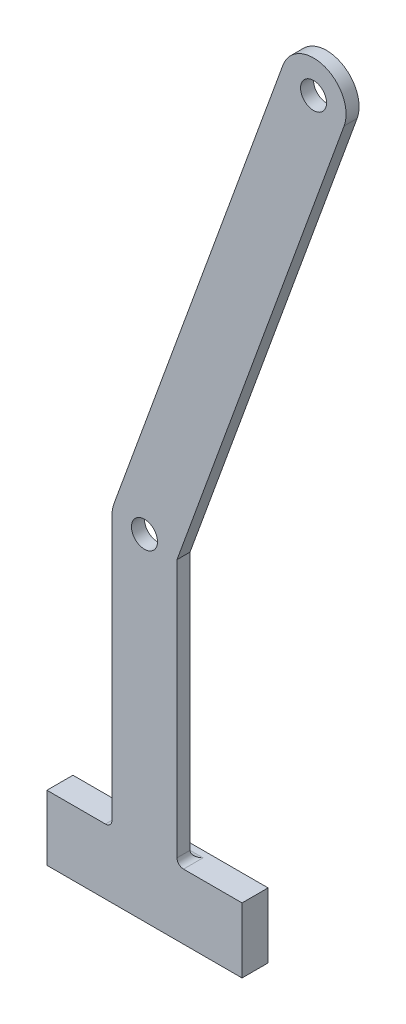
SolidWorks part; units mm, degrees
ref_plane "Front Plane" through (0, 0, 0) normal (0, 0, 1) x (1, 0, 0)
ref_plane "Top Plane" through (0, 0, 0) normal (0, 1, 0) x (1, 0, 0)
ref_plane "Right Plane" through (0, 0, 0) normal (1, 0, 0) x (0, 0, -1)
sketch "Sketch1" plane through (0, 0, 0) normal (0, 0, 1) x (1, 0, 0)
  line L0 (-76.2, 0) -> (-76.2, -95.25) construction
  line L1 (-27.94, -19.05) -> (-124.46, -19.05) construction
  line L2 (-27.94, -19.05) -> (-27.94, -171.45) construction
  line L3 (-27.94, -171.45) -> (-124.46, -171.45) construction
  line L4 (-124.46, -19.05) -> (-124.46, -171.45) construction
  line L5 (-27.94, -19.05) -> (-124.46, -171.45) construction
  line L6 (-27.94, -171.45) -> (-124.46, -19.05) construction
  line L7 (0, 0) -> (-76.2, 0) construction
  line L8 (-27.94, -19.05) -> (-60.9518, -109.7491) construction
  line L9 (-21.973, -21.2218) -> (-54.9847, -111.921)
  line L10 (-33.907, -16.8782) -> (-66.9188, -107.5773)
  line L11 (-27.94, -19.05) -> (-20.32, -19.05) construction
  line L12 (-60.9518, -19.05) -> (-60.9518, -162.56) construction
  line L13 (-67.3018, -109.7491) -> (-67.3018, -162.56)
  line L14 (-54.6018, -109.7491) -> (-54.6018, -162.56)
  line L15 (-67.3018, -162.56) -> (-80.0018, -162.56)
  line L16 (-80.0018, -162.56) -> (-80.0018, -175.26)
  line L17 (-80.0018, -175.26) -> (-41.9018, -175.26)
  line L18 (-41.9018, -175.26) -> (-41.9018, -162.56)
  line L19 (-41.9018, -162.56) -> (-54.6018, -162.56)
  circle A0 centre (-27.94, -19.05) radius 2.54
  circle A1 centre (-124.46, -19.05) radius 2.54
  circle A2 centre (-124.46, -171.45) radius 2.54
  circle A3 centre (-27.94, -171.45) radius 2.54
  circle A4 centre (-60.9518, -109.7491) radius 2.54
  circle A5 centre (-27.94, -19.05) radius 6.35
  circle A6 centre (-60.9518, -109.7491) radius 6.35
  dimension "D4" = 5.08
  dimension "D6" = 5.08
  dimension "D9" = 3.81
  dimension "D10" = 5.08
  dimension "D11" = 3.81
  dimension "D1" = 95.25
  dimension "D2" = 76.2
  dimension "D3" = 152.4
  dimension "D5" = 96.52
  dimension "D7" = 96.52
  dimension "D8" = 20
  dimension "D12" = 7.62
  dimension "D13" = 143.51
  dimension "D14" = 38.1
  dimension "D15" = 12.7
  dimension "D16" = 12.7
extrude "Boss-Extrude1" add sketch "Sketch1" along normal blind 2.54 contours A6 L9 A5 L10 | A5 A0 | A6 A4 | A6 L13 L15 L16 L17 L18 L19 L14 L9 | A6 L9 L14
sketch "Sketch2" plane through (0, 0, 0) normal (0, 0, -1) x (-1, 0, 0)
  line L1 (41.9018, -162.56) -> (80.0018, -162.56)
  line L2 (41.9018, -162.56) -> (41.9018, -175.26)
  line L3 (41.9018, -175.26) -> (80.0018, -175.26)
  line L4 (80.0018, -162.56) -> (80.0018, -175.26)
  line L5 (41.9018, -162.56) -> (80.0018, -175.26) construction
  line L6 (41.9018, -175.26) -> (80.0018, -162.56) construction
  point P4 (60.9518, -168.91)
extrude "Boss-Extrude2" add sketch "Sketch2" along normal blind 2.54
fillet "Fillet1" radius 1.27 3 edges at (-60.9518, -162.56, 0) (-54.6018, -162.56, 1.27) (-67.3018, -162.56, 1.27)
